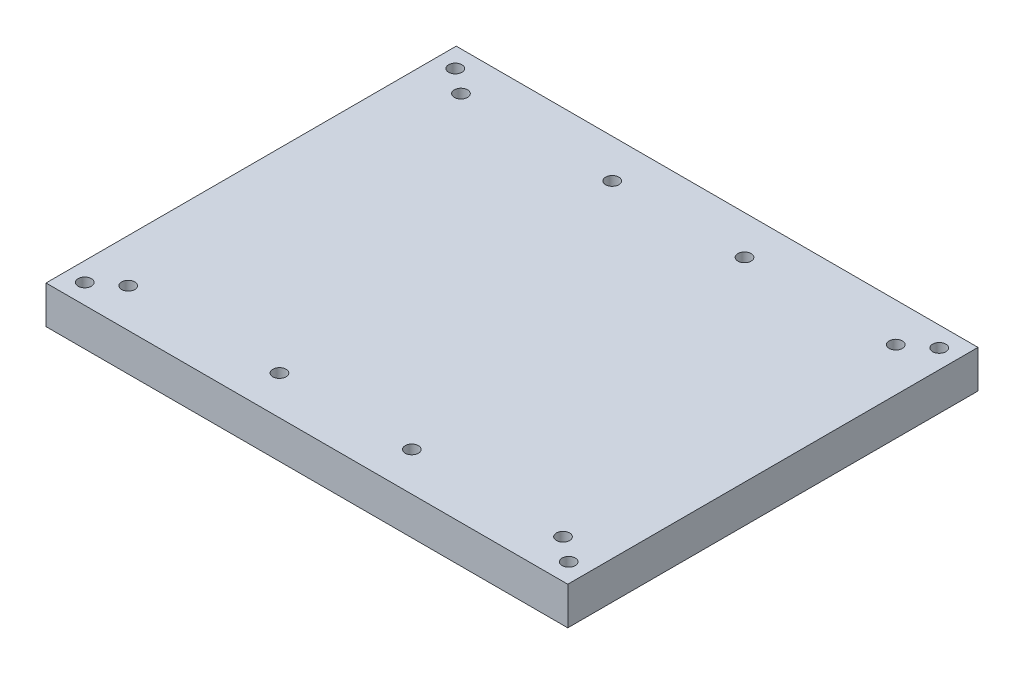
SolidWorks part; units mm, degrees
ref_plane "Front" through (0, 0, 0) normal (0, 0, 1) x (1, 0, 0)
ref_plane "Top" through (0, 0, 0) normal (0, 1, 0) x (1, 0, 0)
ref_plane "Right" through (0, 0, 0) normal (1, 0, 0) x (0, 0, -1)
sketch "Sketch1" plane through (0, 0, 0) normal (0, 1, 0) x (1, 0, 0)
  line L0 (-37.5, 0) -> (0, 0) construction
  line L1 (69, -54.25) -> (-69, -54.25)
  line L2 (69, -54.25) -> (69, 54.25)
  line L3 (69, 54.25) -> (-69, 54.25)
  line L4 (-69, -54.25) -> (-69, 54.25)
  line L5 (69, -54.25) -> (-69, 54.25) construction
  line L6 (69, 54.25) -> (-69, -54.25) construction
  line L7 (64, -49) -> (-64, -49) construction
  line L8 (64, -49) -> (64, 49) construction
  line L9 (64, 49) -> (-64, 49) construction
  line L10 (-64, -49) -> (-64, 49) construction
  line L11 (64, -49) -> (-64, 49) construction
  line L12 (64, 49) -> (-64, -49) construction
  line L13 (-17.5, -44) -> (-57.5, -44) construction
  line L14 (-17.5, -44) -> (-17.5, 44) construction
  line L15 (-17.5, 44) -> (-57.5, 44) construction
  line L16 (-57.5, -44) -> (-57.5, 44) construction
  line L17 (-17.5, -44) -> (-57.5, 44) construction
  line L18 (-17.5, 44) -> (-57.5, -44) construction
  line L19 (57.5, -44) -> (17.5, -44) construction
  line L20 (57.5, -44) -> (57.5, 44) construction
  line L21 (57.5, 44) -> (17.5, 44) construction
  line L22 (17.5, -44) -> (17.5, 44) construction
  line L23 (57.5, -44) -> (17.5, 44) construction
  line L24 (57.5, 44) -> (17.5, -44) construction
  line L25 (0, 0) -> (37.5, 0) construction
  circle A0 centre (-64, 49) radius 1.75
  circle A1 centre (-64, -49) radius 1.75
  circle A2 centre (64, -49) radius 1.75
  circle A3 centre (64, 49) radius 1.75
  circle A4 centre (-57.5, 44) radius 1.75
  circle A5 centre (-17.5, 44) radius 1.75
  circle A6 centre (-17.5, -44) radius 1.75
  circle A7 centre (-57.5, -44) radius 1.75
  circle A8 centre (17.5, -44) radius 1.75
  circle A9 centre (57.5, -44) radius 1.75
  circle A10 centre (57.5, 44) radius 1.75
  circle A11 centre (17.5, 44) radius 1.75
  point P0 (0, 0)
  point P6 (0, 0)
  point P15 (-37.5, 0)
  point P20 (37.5, 0)
  dimension "D3" = 3.5
  dimension "D1" = 138
  dimension "D2" = 108.5
  dimension "D4" = 128
  dimension "D5" = 98
  dimension "D6" = 88
  dimension "D7" = 40
  dimension "D8" = 75
extrude "Boss-Extrude1" add sketch "Sketch1" along normal blind 10
